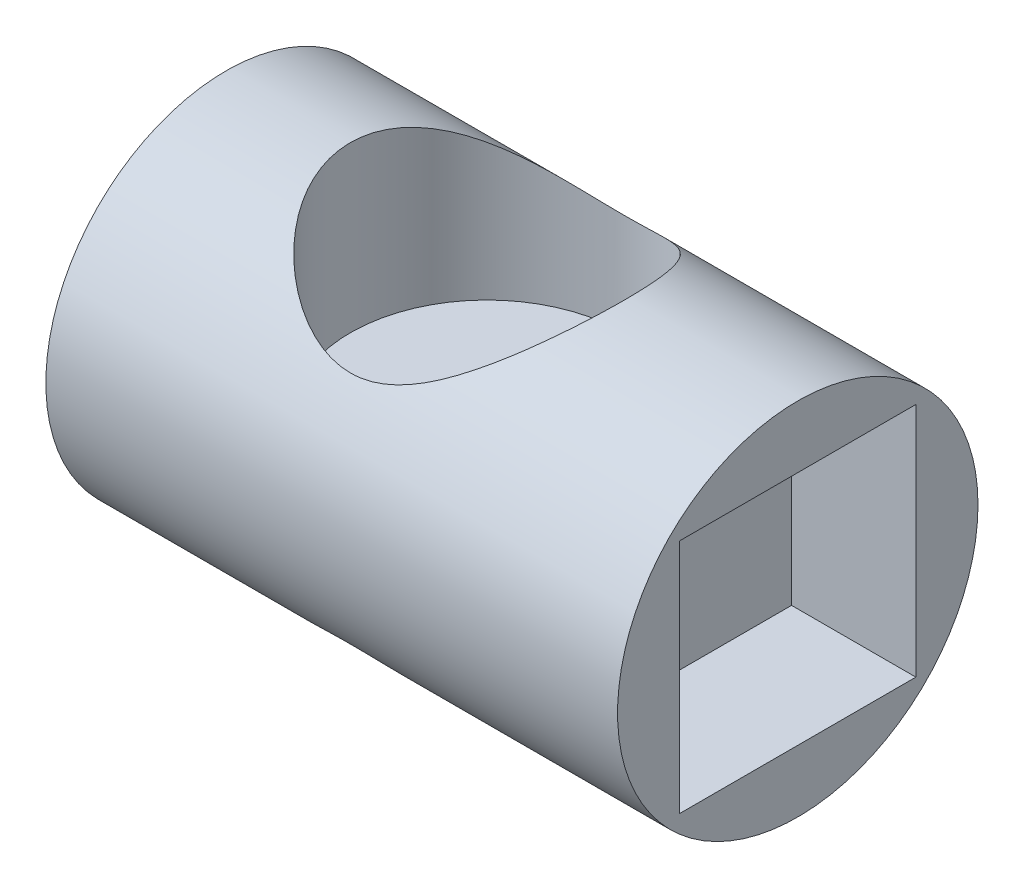
SolidWorks part; units mm, degrees
ref_plane "Alzado" through (0, 0, 0) normal (0, 0, 1) x (1, 0, 0)
ref_plane "Planta" through (0, 0, 0) normal (0, 1, 0) x (1, 0, 0)
ref_plane "Vista lateral" through (0, 0, 0) normal (1, 0, 0) x (0, 0, -1)
sketch "Croquis1" plane through (0, 0, 0) normal (1, 0, 0) x (0, 0, -1)
  circle A0 centre (0, 0) radius 14.5
  dimension "D1" = 29
extrude "Saliente-Extruir1" add sketch "Croquis1" along normal blind 46
sketch "Croquis2" plane through (0, 0, 0) normal (-1, 0, 0) x (0, 0, 1)
  circle A0 centre (0, 0) radius 4
  dimension "D1" = 8
extrude "Cortar-Extruir1" cut sketch "Croquis2" against normal blind 8
sketch "Croquis3" plane through (0, 0, 0) normal (0, 1, 0) x (1, 0, 0)
  line L0 (46, 0) -> (0, 0) construction
  line L1 (46, -14.5) -> (46, 14.5) construction
  circle A1 centre (21, 0) radius 11
  dimension "D1" = 22
  dimension "D2" = 25
  dimension "D3" = 46
extrude "Cortar-Extruir2" cut sketch "Croquis3" against normal through all both and the other way through all
sketch "Croquis4" plane through (46, 0, 0) normal (1, 0, 0) x (0, 0, -1)
  line L1 (-9.5, -9.5) -> (9.5, -9.5)
  line L2 (-9.5, -9.5) -> (-9.5, 9.5)
  line L3 (-9.5, 9.5) -> (9.5, 9.5)
  line L4 (9.5, -9.5) -> (9.5, 9.5)
  line L5 (-9.5, -9.5) -> (9.5, 9.5) construction
  line L6 (-9.5, 9.5) -> (9.5, -9.5) construction
  point P0 (0, 0)
  dimension "D1" = 19
  dimension "D2" = 19
extrude "Cortar-Extruir3" cut sketch "Croquis4" against normal blind 10
sketch "Croquis5" plane through (36, 0, 0) normal (1, 0, 0) x (0, 0, -1)
  line L0 (9.5, -9.5) -> (9.5, 9.5) construction
  line L1 (-9.5, -1.25) -> (9.5, -1.25)
  line L2 (-9.5, -1.25) -> (-9.5, 1.25)
  line L3 (-9.5, 1.25) -> (9.5, 1.25)
  line L4 (9.5, -1.25) -> (9.5, 1.25)
  line L5 (-9.5, -1.25) -> (9.5, 1.25) construction
  line L6 (-9.5, 1.25) -> (9.5, -1.25) construction
  point P0 (0, 0)
  dimension "D1" = 2.5
extrude "Saliente-Extruir2" add sketch "Croquis5" against normal up to surface (28 mm away) up to face at (8, 0, 4)
sketch "Croquis7" plane through (0, -1.25, 0) normal (0, -1, 0) x (1, 0, 0)
  line L0 (21, 9.5) -> (21, -9.5) construction
  line L1 (15.4547, 9.5) -> (26.5453, 9.5) construction
  line L2 (15.4547, -9.5) -> (26.5453, -9.5) construction
  circle A0 centre (21, 0) radius 11.15
  dimension "D1" = 22.3
extrude "Saliente-Extruir3" add sketch "Croquis7" against normal blind 2.5
